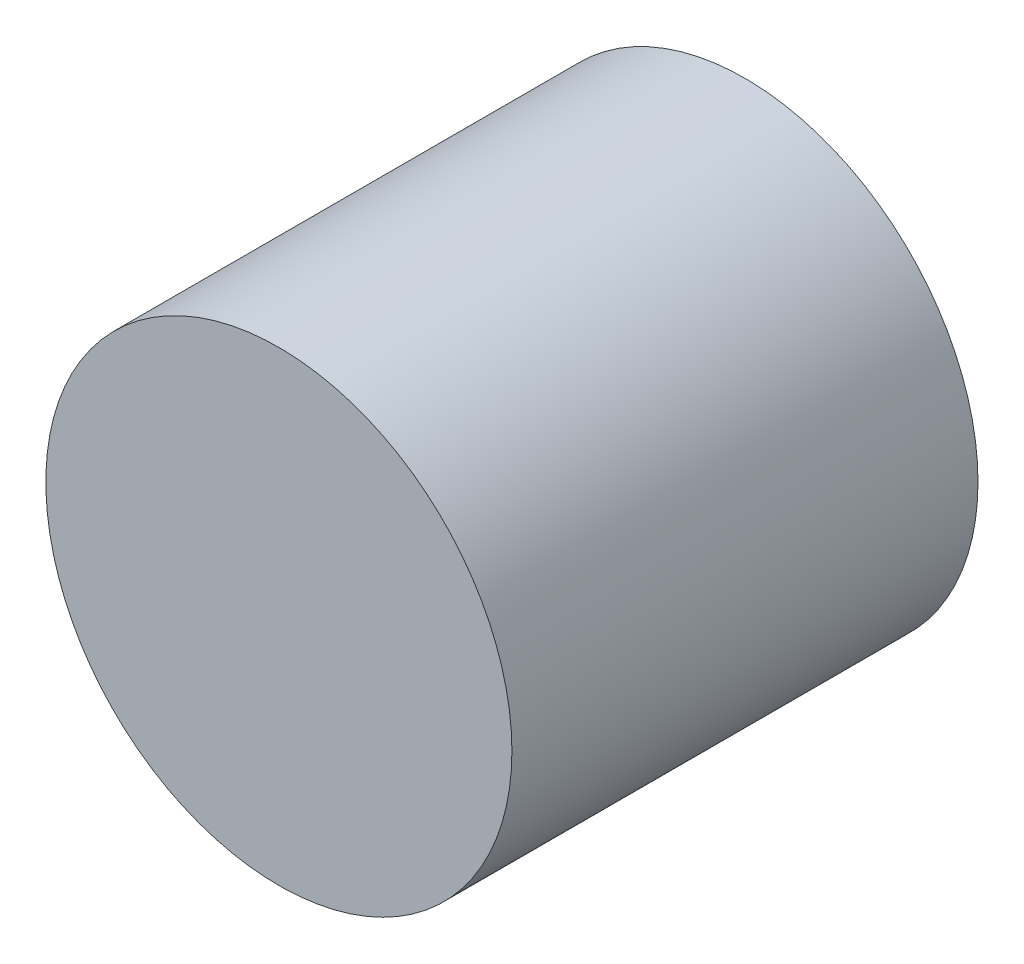
SolidWorks part; units mm, degrees
ref_plane "前视基准面" through (0, 0, 0) normal (0, 0, 1) x (1, 0, 0)
ref_plane "上视基准面" through (0, 0, 0) normal (0, 1, 0) x (1, 0, 0)
ref_plane "右视基准面" through (0, 0, 0) normal (1, 0, 0) x (0, 0, -1)
other "Configuration Table"
sketch "草图1" plane through (0, 0, 0) normal (0, 0, 1) x (1, 0, 0)
  circle A0 centre (0, 0) radius 5
  dimension "D1" = 10
extrude "凸台-拉伸1" add sketch "草图1" along normal blind 10
